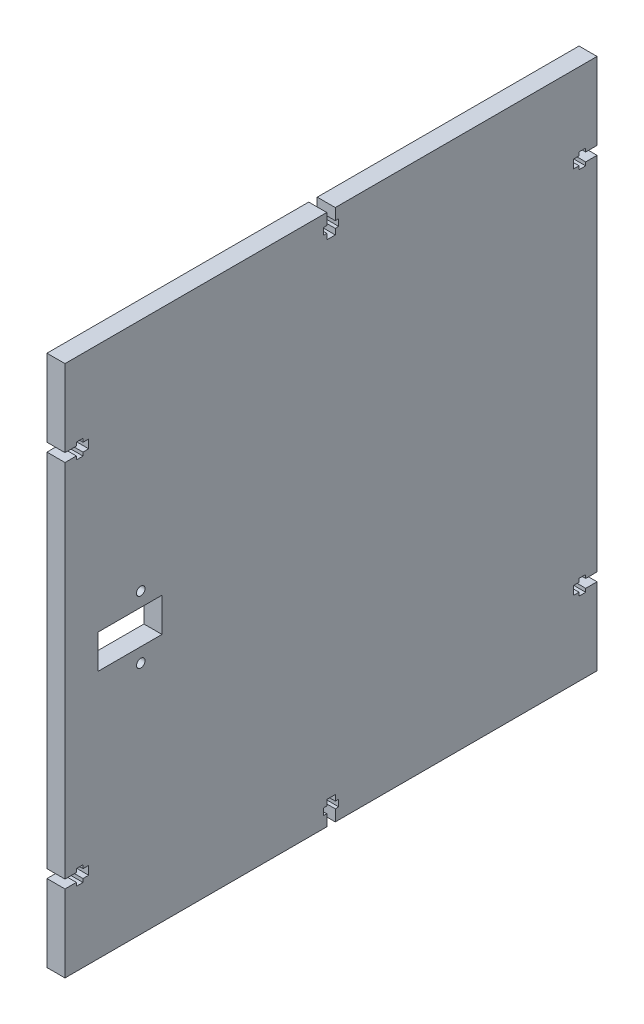
SolidWorks part; units mm, degrees
ref_plane "Front" through (0, 0, 0) normal (0, 0, 1) x (1, 0, 0)
ref_plane "Top" through (0, 0, 0) normal (0, 1, 0) x (1, 0, 0)
ref_plane "Right" through (0, 0, 0) normal (1, 0, 0) x (0, 0, -1)
sketch "Sketch1" plane through (0, 0, 0) normal (1, 0, 0) x (0, 0, -1)
  line L1 (-93.65, -93.65) -> (93.65, -93.65)
  line L2 (-93.65, -93.65) -> (-93.65, 93.65)
  line L3 (-93.65, 93.65) -> (93.65, 93.65)
  line L4 (93.65, -93.65) -> (93.65, 93.65)
  line L5 (-93.65, -93.65) -> (93.65, 93.65) construction
  line L6 (-93.65, 93.65) -> (93.65, -93.65) construction
  point P0 (0, 0)
  dimension "D1" = 187.3
  dimension "D2" = 187.3
extrude "Boss-Extrude1" add sketch "Sketch1" along normal blind 6.35
sketch "Sketch2" plane through (6.35, 0, 0) normal (1, 0, 0) x (0, 0, -1)
  line L1 (-82.059, 5.975) -> (-59.509, 5.975)
  line L2 (-82.059, 5.975) -> (-82.059, -5.975)
  line L3 (-82.059, -5.975) -> (-59.509, -5.975)
  line L4 (-59.509, 5.975) -> (-59.509, -5.975)
  point P4 (-59.509, 0)
  dimension "D1" = 22.55
  dimension "D2" = 11.95
extrude "Cut-Extrude1" cut sketch "Sketch2" against normal blind 6.35
sketch "Sketch3" plane through (6.35, 0, 0) normal (1, 0, 0) x (0, 0, -1)
  line L0 (-66.979, 11) -> (-66.979, -11) construction
  line L1 (-82.059, 5.975) -> (-82.059, -5.975) construction
  line L2 (-59.509, -5.975) -> (-59.509, 5.975) construction
  circle A0 centre (-66.979, 11) radius 1.5
  circle A1 centre (-66.979, -11) radius 1.5
  point P6 (-82.059, 0)
  point P7 (-66.979, 0)
  dimension "D3" = 3
  dimension "D1" = 22
  dimension "D2" = 7.47
extrude "Cut-Extrude2" cut sketch "Sketch3" against normal through all
sketch "Sketch4" plane through (6.35, 0, 0) normal (1, 0, 0) x (0, 0, -1)
  line L0 (-93.65, 93.65) -> (-93.65, -93.65) construction
  line L1 (-93.65, 66.5) -> (-89.65, 66.5)
  line L2 (-93.65, 66.5) -> (-93.65, 63.5)
  line L3 (-93.65, 63.5) -> (-89.65, 63.5)
  line L5 (-89.65, 63.5) -> (-89.65, 62.29)
  line L6 (-89.65, 67.71) -> (-87.3, 67.71)
  line L7 (-89.65, 67.71) -> (-89.65, 66.5)
  line L8 (-89.65, 62.29) -> (-87.3, 62.29)
  line L9 (-87.3, 67.71) -> (-87.3, 66.5)
  line L10 (-87.3, 66.5) -> (-85.3, 66.5)
  line L12 (-87.3, 63.5) -> (-85.3, 63.5)
  line L13 (-85.3, 66.5) -> (-85.3, 63.5)
  line L14 (-87.3, 63.5) -> (-87.3, 62.29)
  line L15 (-93.65, 0) -> (93.65, 0) construction
  line L16 (93.65, -93.65) -> (93.65, 93.65) construction
  line L17 (-87.3, -63.5) -> (-87.3, -62.29)
  line L18 (-85.3, -66.5) -> (-85.3, -63.5)
  line L19 (-87.3, -63.5) -> (-85.3, -63.5)
  line L20 (-87.3, -66.5) -> (-85.3, -66.5)
  line L21 (-87.3, -67.71) -> (-87.3, -66.5)
  line L22 (-89.65, -62.29) -> (-87.3, -62.29)
  line L23 (-89.65, -67.71) -> (-89.65, -66.5)
  line L24 (-89.65, -67.71) -> (-87.3, -67.71)
  line L25 (-89.65, -63.5) -> (-89.65, -62.29)
  line L26 (-93.65, -63.5) -> (-89.65, -63.5)
  line L27 (-93.65, -66.5) -> (-93.65, -63.5)
  line L28 (-93.65, -66.5) -> (-89.65, -66.5)
  line L29 (0, 93.65) -> (0, -93.65) construction
  line L30 (93.65, 93.65) -> (-93.65, 93.65) construction
  line L31 (-93.65, -93.65) -> (93.65, -93.65) construction
  line L32 (93.65, -66.5) -> (89.65, -66.5)
  line L33 (93.65, -66.5) -> (93.65, -63.5)
  line L34 (93.65, -63.5) -> (89.65, -63.5)
  line L35 (89.65, -63.5) -> (89.65, -62.29)
  line L36 (89.65, -67.71) -> (87.3, -67.71)
  line L37 (89.65, -67.71) -> (89.65, -66.5)
  line L38 (89.65, -62.29) -> (87.3, -62.29)
  line L39 (87.3, -67.71) -> (87.3, -66.5)
  line L40 (87.3, -66.5) -> (85.3, -66.5)
  line L41 (87.3, -63.5) -> (85.3, -63.5)
  line L42 (85.3, -66.5) -> (85.3, -63.5)
  line L43 (87.3, -63.5) -> (87.3, -62.29)
  line L44 (87.3, 63.5) -> (87.3, 62.29)
  line L45 (85.3, 66.5) -> (85.3, 63.5)
  line L46 (87.3, 63.5) -> (85.3, 63.5)
  line L47 (87.3, 66.5) -> (85.3, 66.5)
  line L48 (87.3, 67.71) -> (87.3, 66.5)
  line L49 (89.65, 62.29) -> (87.3, 62.29)
  line L50 (89.65, 67.71) -> (89.65, 66.5)
  line L51 (89.65, 67.71) -> (87.3, 67.71)
  line L52 (89.65, 63.5) -> (89.65, 62.29)
  line L53 (93.65, 63.5) -> (89.65, 63.5)
  line L54 (93.65, 66.5) -> (93.65, 63.5)
  line L55 (93.65, 66.5) -> (89.65, 66.5)
  line L56 (-1.5, 93.65) -> (-1.5, 89.65)
  line L57 (2.71, 89.65) -> (2.71, 87.3)
  line L58 (1.5, 93.65) -> (1.5, 89.65)
  line L59 (1.5, 87.3) -> (2.71, 87.3)
  line L60 (-2.71, 89.65) -> (-1.5, 89.65)
  line L61 (-1.5, 87.3) -> (-1.5, 85.3)
  line L62 (-1.5, 93.65) -> (1.5, 93.65)
  line L63 (-2.71, 89.65) -> (-2.71, 87.3)
  line L64 (1.5, 87.3) -> (1.5, 85.3)
  line L65 (1.5, 89.65) -> (2.71, 89.65)
  line L66 (-1.5, 85.3) -> (1.5, 85.3)
  line L67 (-2.71, 87.3) -> (-1.5, 87.3)
  line L68 (-2.71, -87.3) -> (-1.5, -87.3)
  line L69 (-1.5, -85.3) -> (1.5, -85.3)
  line L70 (1.5, -89.65) -> (2.71, -89.65)
  line L71 (1.5, -87.3) -> (1.5, -85.3)
  line L72 (-2.71, -89.65) -> (-2.71, -87.3)
  line L73 (-1.5, -93.65) -> (1.5, -93.65)
  line L74 (-1.5, -87.3) -> (-1.5, -85.3)
  line L75 (-2.71, -89.65) -> (-1.5, -89.65)
  line L76 (1.5, -87.3) -> (2.71, -87.3)
  line L77 (1.5, -93.65) -> (1.5, -89.65)
  line L78 (2.71, -89.65) -> (2.71, -87.3)
  line L79 (-1.5, -93.65) -> (-1.5, -89.65)
  point P14 (-86.3, 66.5)
  point P19 (-93.65, 65)
  point P87 (1.5, 86.3)
  dimension "D1" = 3
  dimension "D2" = 5.42
  dimension "D3" = 2
  dimension "D4" = 4
  dimension "D5" = 2.35
  dimension "D6" = 65
  dimension "D7" = 3
extrude "Cut-Extrude3" cut sketch "Sketch4" against normal through all
